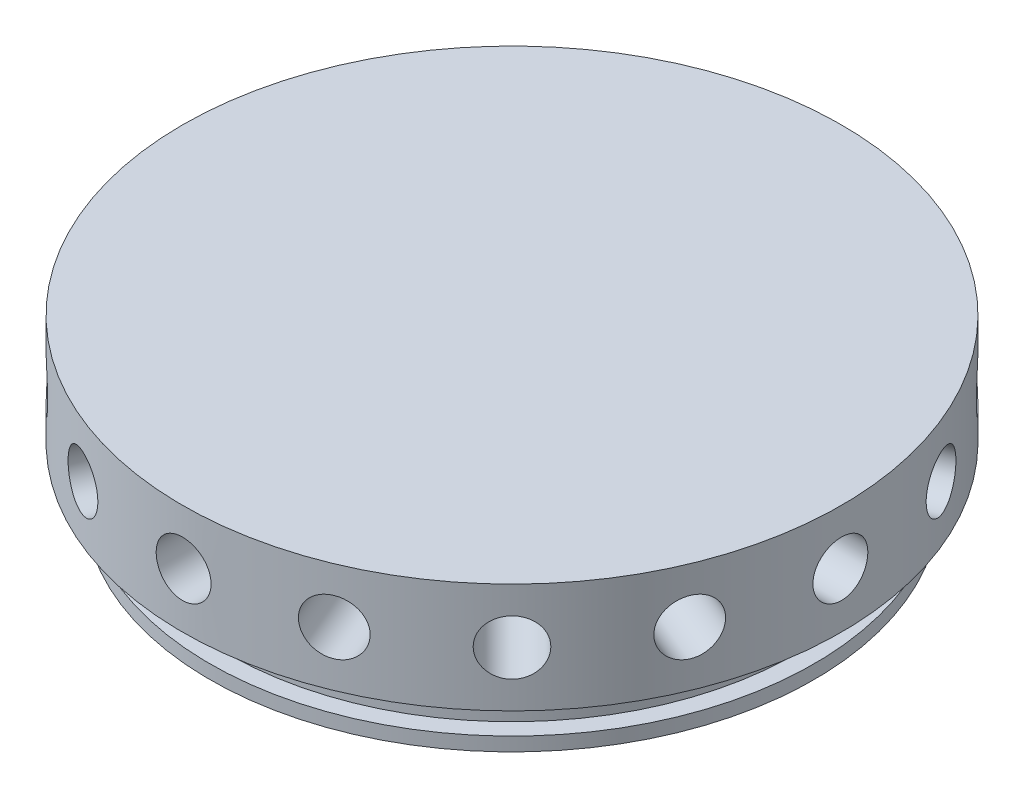
SolidWorks part; units mm, degrees
ref_plane "Front Plane" through (0, 0, 0) normal (0, 0, 1) x (1, 0, 0)
ref_plane "Top Plane" through (0, 0, 0) normal (0, 1, 0) x (1, 0, 0)
ref_plane "Right Plane" through (0, 0, 0) normal (1, 0, 0) x (0, 0, -1)
ref_axis "Axis1" through (0, 20.0025, 0) along (0, -1, 0)
sketch "Sketch1" plane through (0, 0, 0) normal (0, 0, 1) x (1, 0, 0)
  line L0 (0, 0) -> (-34.925, 0)
  line L1 (-34.925, 0) -> (-34.925, 1.5875)
  line L2 (-34.925, 1.5875) -> (-32.893, 1.5875)
  line L3 (-32.893, 1.5875) -> (-32.893, 4.3307)
  line L4 (-32.893, 4.3307) -> (-34.925, 4.3307)
  line L5 (-34.925, 4.3307) -> (-34.925, 6.35)
  line L6 (-34.925, 6.35) -> (-38.1, 6.35)
  line L7 (-38.1, 6.35) -> (-38.1, 19.05)
  line L8 (-38.1, 19.05) -> (0, 19.05)
  line L9 (0, 19.05) -> (0, 0)
  dimension "D1" = 2.7432
  dimension "D2" = 2.032
  dimension "D3" = 1.5875
  dimension "D4" = 19.05
  dimension "D5" = 12.7
  dimension "D6" = 3.175
  dimension "D7" = 34.925
revolve "Revolve1" add sketch "Sketch1" angle 360 about L9
ref_plane "Plane1" through (-38.1, 0, 0) normal (-1, 0, 0) x (0, 0, 1)
hole_wizard "1/4 (0.25) Diameter Hole1" positions "Sketch2" profile "Sketch3" hole size "1/4" standard "ANSI Inch"
sketch "Sketch2" plane through (-38.1, 0, 0) normal (-1, 0, 0) x (0, 0, 1)
  point P0 (0, 12.7)
  dimension "D1" = 12.7
sketch "Sketch3" plane through (-38.1, 12.7, 0) normal (0, 1, 0) x (0, 0, 1)
  line L0 (0, 0) -> (0, 14.6077)
  line L1 (0, 14.6077) -> (3.175, 12.7)
  line L2 (3.175, 12.7) -> (3.175, 0)
  line L5 (3.175, 0) -> (0, 0)
  line L10 (0, 14.6077) -> (-3.175, 12.7) construction
  line L11 (0, -6.35) -> (0, 107.95) construction
  dimension "Hole Dia." = 6.35
  dimension "Hole Depth" = 12.7
  dimension "Drill Angle" = 118
hole_wizard "3/16 (0.1875) Diameter Hole2" positions "Sketch4" profile "Sketch5" hole size "3/16" standard "ANSI Inch"
sketch "Sketch4" plane through (-38.1, 0, 0) normal (-1, 0, 0) x (0, 0, 1)
  point P0 (0, 12.7)
sketch "Sketch5" plane through (-38.1, 12.7, 0) normal (0, 1, 0) x (0, 0, 1)
  line L0 (0, 0) -> (0, 25.2433)
  line L1 (0, 25.2433) -> (2.3812, 23.8125)
  line L2 (2.3812, 23.8125) -> (2.3812, 0)
  line L5 (2.3812, 0) -> (0, 0)
  line L10 (0, 25.2433) -> (-2.3813, 23.8125) construction
  line L11 (0, -6.35) -> (0, 107.95) construction
  dimension "Hole Dia." = 4.7625
  dimension "Hole Depth" = 23.8125
  dimension "Drill Angle" = 118
hole_wizard "1/8 (0.125) Diameter Hole1" positions "Sketch6" profile "Sketch7" hole size "1/8" standard "ANSI Inch"
sketch "Sketch6" plane through (-38.1, 0, 0) normal (-1, 0, 0) x (0, 0, 1)
  point P0 (0, 12.7)
sketch "Sketch7" plane through (-38.1, 12.7, 0) normal (0, 1, 0) x (0, 0, 1)
  line L0 (0, 0) -> (0, 34.2914)
  line L1 (0, 34.2914) -> (1.5875, 33.3375)
  line L2 (1.5875, 33.3375) -> (1.5875, 0)
  line L5 (1.5875, 0) -> (0, 0)
  line L10 (0, 34.2914) -> (-1.5875, 33.3375) construction
  line L11 (0, -6.35) -> (0, 107.95) construction
  dimension "Hole Dia." = 3.175
  dimension "Hole Depth" = 33.3375
  dimension "Drill Angle" = 118
pattern_circular "CirPattern1" count 16 over 360 about axis through (0, 20.0025, 0) along (0, -1, 0) of "1/4 (0.25) Diameter Hole1"
pattern_circular "CirPattern2" count 8 over 360 about axis through (0, 20.0025, 0) along (0, -1, 0) of "3/16 (0.1875) Diameter Hole2"
pattern_circular "CirPattern3" count 4 over 360 about axis through (0, 20.0025, 0) along (0, -1, 0) of "1/8 (0.125) Diameter Hole1"
